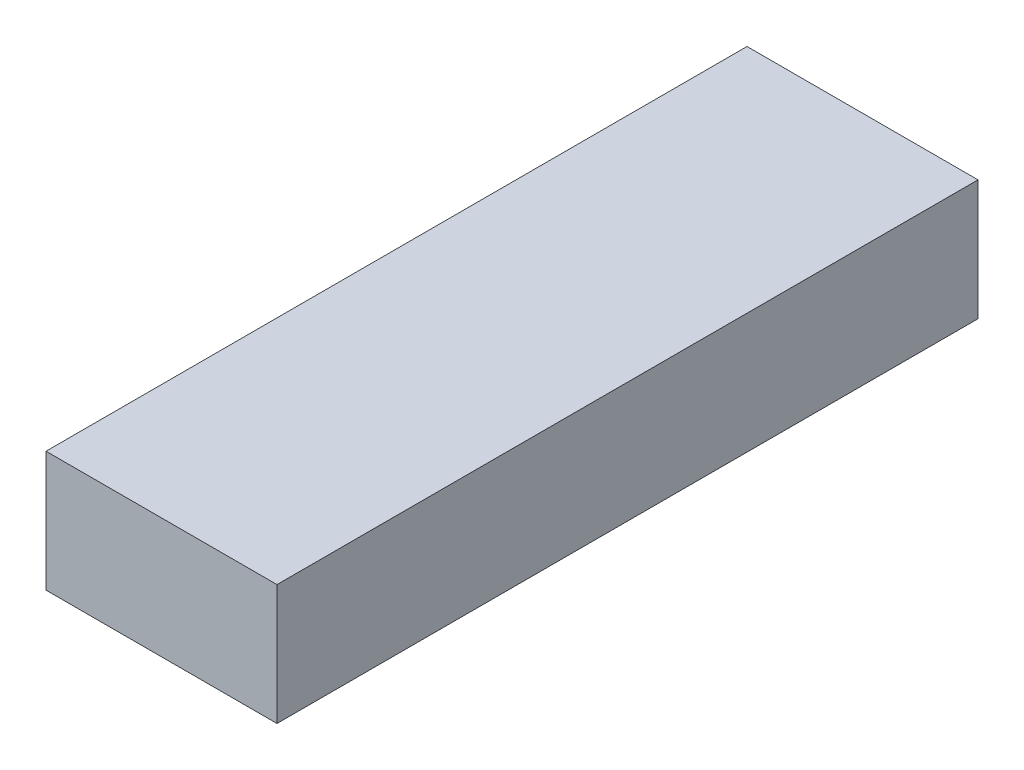
SolidWorks part; units mm, degrees
ref_plane "正面" through (0, 0, 0) normal (0, 0, 1) x (1, 0, 0)
ref_plane "平面" through (0, 0, 0) normal (0, 1, 0) x (1, 0, 0)
ref_plane "右側面" through (0, 0, 0) normal (1, 0, 0) x (0, 0, -1)
sketch "ｽｹｯﾁ1" plane through (0, 0, 0) normal (0, 0, 1) x (1, 0, 0)
  line L1 (-18.637, 10.1345) -> (24.363, 10.1345)
  line L2 (-18.637, 10.1345) -> (-18.637, -12.2655)
  line L3 (-18.637, -12.2655) -> (24.363, -12.2655)
  line L4 (24.363, 10.1345) -> (24.363, -12.2655)
  dimension "D1" = 43
  dimension "D2" = 22.4
extrude "ﾎﾞｽ - 押し出し1" add sketch "ｽｹｯﾁ1" along normal blind 130.5
